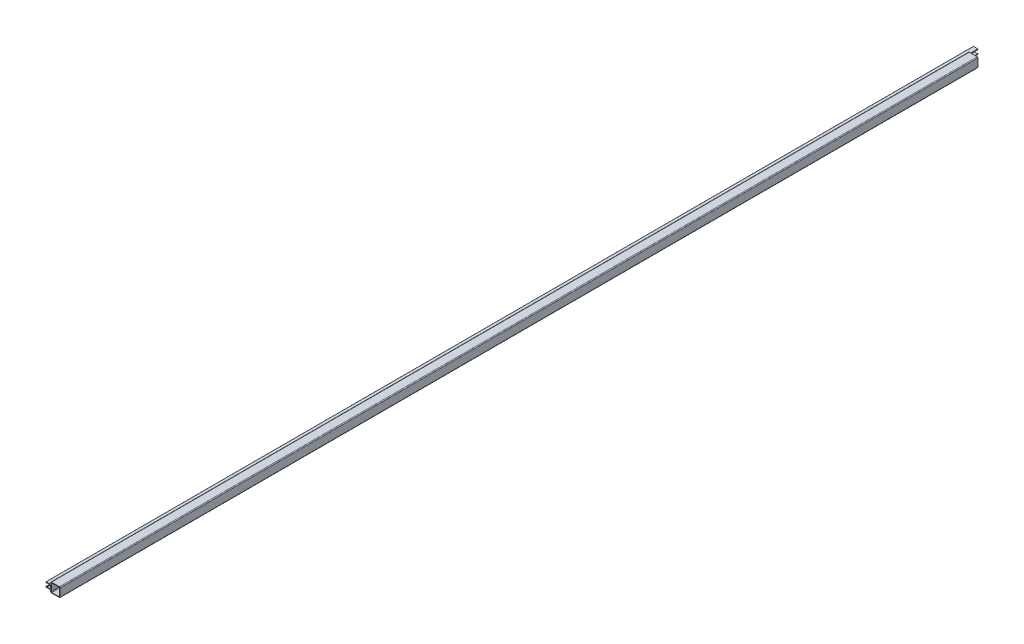
SolidWorks part; units mm, degrees
material "6061 Alloy"
ref_plane "Front Plane" through (0, 0, 0) normal (0, 0, 1) x (1, 0, 0)
ref_plane "Top Plane" through (0, 0, 0) normal (0, 1, 0) x (1, 0, 0)
ref_plane "Right Plane" through (0, 0, 0) normal (1, 0, 0) x (0, 0, -1)
ref_plane "Plane1" through (0, 0, -3683) normal (0, 0, -1) x (-1, 0, 0)
sketch "Sketch1" plane through (0, 0, -3683) normal (0, 0, -1) x (-1, 0, 0)
  line L0 (11.176, 9.652) -> (11.176, -9.652)
  line L1 (9.652, -11.176) -> (-9.652, -11.176)
  line L2 (-11.176, -9.652) -> (-11.176, 9.652)
  line L3 (-9.652, 11.176) -> (9.652, 11.176)
  line L4 (25.4, -5.969) -> (25.4, -4.826)
  line L5 (24.638, -4.064) -> (23.0632, -4.064)
  line L6 (22.3012, -4.826) -> (13.081, -4.826)
  line L7 (12.7, -4.445) -> (12.7, 4.445)
  line L8 (13.081, 4.826) -> (22.3012, 4.826)
  line L9 (23.0632, 4.064) -> (24.638, 4.064)
  line L10 (25.4, 4.826) -> (25.4, 5.969)
  line L11 (25.019, 6.35) -> (13.081, 6.35)
  line L12 (12.7, 6.731) -> (12.7, 10.5918)
  line L13 (10.5918, 12.7) -> (-10.5918, 12.7)
  line L14 (-12.7, 10.5918) -> (-12.7, -10.5918)
  line L15 (-10.5918, -12.7) -> (10.5918, -12.7)
  line L16 (12.7, -10.5918) -> (12.7, -6.731)
  line L17 (13.081, -6.35) -> (25.019, -6.35)
  arc A0 (9.652, 11.176) -> (11.176, 9.652) centre (9.652, 9.652) cw
  arc A1 (11.176, -9.652) -> (9.652, -11.176) centre (9.652, -9.652) cw
  arc A2 (-9.652, -11.176) -> (-11.176, -9.652) centre (-9.652, -9.652) cw
  arc A3 (-11.176, 9.652) -> (-9.652, 11.176) centre (-9.652, 9.652) cw
  arc A4 (25.4, -4.826) -> (24.638, -4.064) centre (24.638, -4.826) ccw
  arc A5 (23.0632, -4.064) -> (22.6822, -4.445) centre (23.0632, -4.445) ccw
  arc A6 (22.6822, -4.445) -> (22.3012, -4.826) centre (22.3012, -4.445) cw
  arc A7 (13.081, -4.826) -> (12.7, -4.445) centre (13.081, -4.445) cw
  arc A8 (12.7, 4.445) -> (13.081, 4.826) centre (13.081, 4.445) cw
  arc A9 (22.3012, 4.826) -> (22.6822, 4.445) centre (22.3012, 4.445) cw
  arc A10 (22.6822, 4.445) -> (23.0632, 4.064) centre (23.0632, 4.445) ccw
  arc A11 (24.638, 4.064) -> (25.4, 4.826) centre (24.638, 4.826) ccw
  arc A12 (25.4, 5.969) -> (25.019, 6.35) centre (25.019, 5.969) ccw
  arc A13 (13.081, 6.35) -> (12.7, 6.731) centre (13.081, 6.731) cw
  arc A14 (12.7, 10.5918) -> (10.5918, 12.7) centre (10.5918, 10.5918) ccw
  arc A15 (-10.5918, 12.7) -> (-12.7, 10.5918) centre (-10.5918, 10.5918) ccw
  arc A16 (-12.7, -10.5918) -> (-10.5918, -12.7) centre (-10.5918, -10.5918) ccw
  arc A17 (10.5918, -12.7) -> (12.7, -10.5918) centre (10.5918, -10.5918) ccw
  arc A18 (12.7, -6.731) -> (13.081, -6.35) centre (13.081, -6.731) cw
  arc A19 (25.019, -6.35) -> (25.4, -5.969) centre (25.019, -5.969) ccw
extrude "Boss-Extrude1" add sketch "Sketch1" against normal blind 2500
sketch "Sketch2" plane through (0, 0, -3683) normal (0, 0, -1) x (-1, 0, 0)
  line L0 (12.7583, -12.7) -> (12.7583, 12.7)
  line L2 (12.7583, -12.7) -> (-10.5918, -12.7)
  line L3 (-10.5918, -12.7) -> (-12.7, -12.9098)
  line L4 (-12.7, -12.9098) -> (-12.7, 10.5918)
  line L5 (-10.5918, 12.7) -> (10.5918, 12.7)
  line L7 (12.7583, 12.7) -> (10.5918, 12.7)
  arc A0 (-12.7, 10.5918) -> (-10.5918, 12.7) centre (-10.5918, 10.5918) cw
extrude "Cut-Extrude2" cut sketch "Sketch2" against normal blind 25.4
